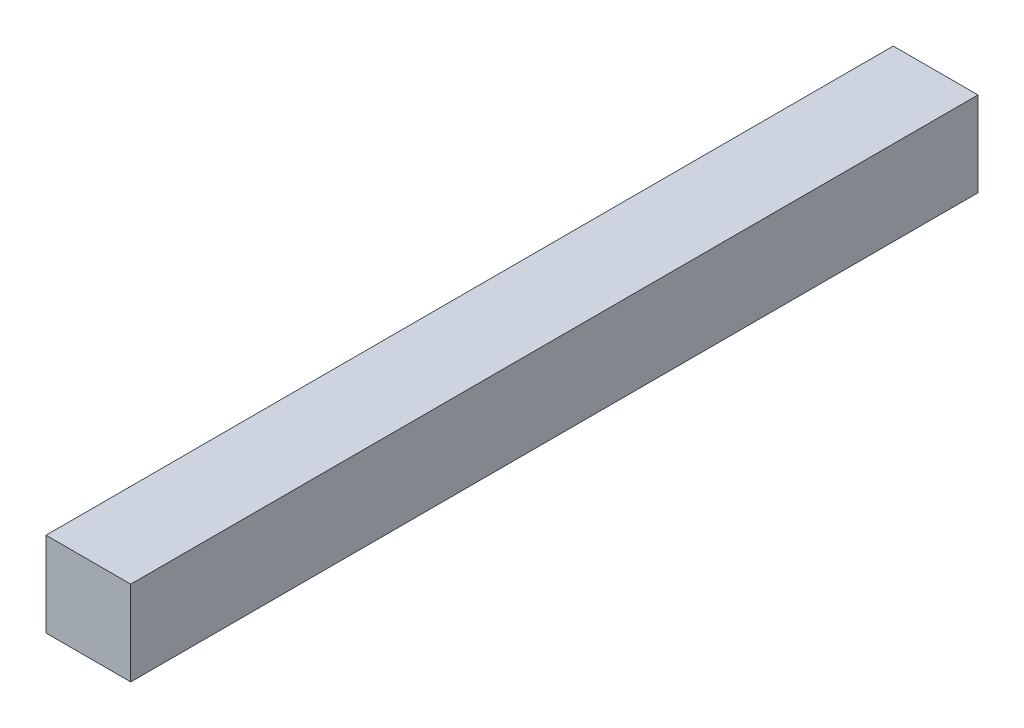
SolidWorks part; units mm, degrees
ref_plane "Front Plane" through (0, 0, 0) normal (0, 0, 1) x (1, 0, 0)
ref_plane "Top Plane" through (0, 0, 0) normal (0, 1, 0) x (1, 0, 0)
ref_plane "Right Plane" through (0, 0, 0) normal (1, 0, 0) x (0, 0, -1)
sketch "Sketch1" plane through (0, 0, 0) normal (0, 0, 1) x (1, 0, 0)
  line L1 (-47.3075, 27.9509) -> (-37.3075, 27.9509)
  line L2 (-47.3075, 27.9509) -> (-47.3075, 17.9509)
  line L3 (-47.3075, 17.9509) -> (-37.3075, 17.9509)
  line L4 (-37.3075, 27.9509) -> (-37.3075, 17.9509)
  dimension "D1" = 10
extrude "Boss-Extrude1" add sketch "Sketch1" along normal blind 100
